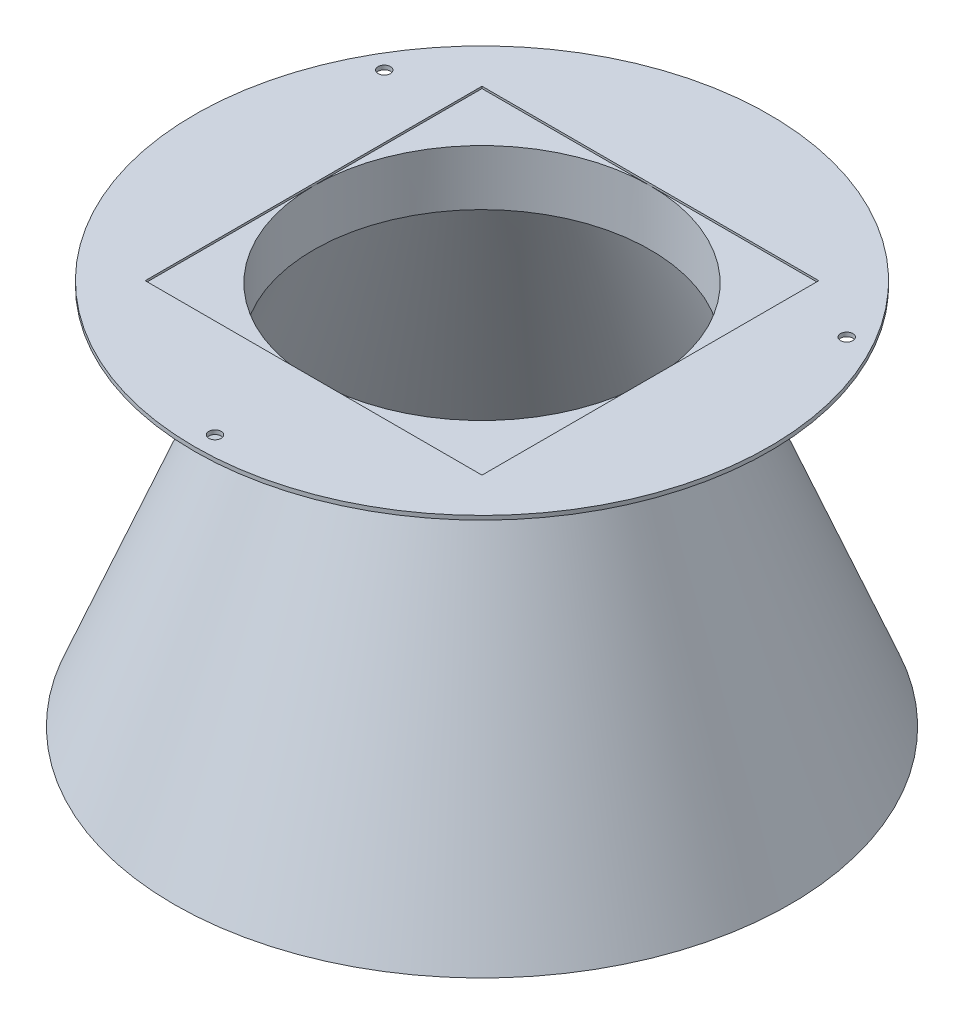
SolidWorks part; units mm, degrees
ref_plane "Alzado" through (0, 0, 0) normal (0, 0, 1) x (1, 0, 0)
ref_plane "Planta" through (0, 0, 0) normal (0, 1, 0) x (1, 0, 0)
ref_plane "Vista lateral" through (0, 0, 0) normal (1, 0, 0) x (0, 0, -1)
sketch "Croquis1" plane through (0, 0, 0) normal (0, 0, 1) x (1, 0, 0)
  line L0 (-67.9016, 46.9761) -> (-67.9016, 60.9761)
  line L1 (-69.9016, 46.9761) -> (-69.9016, -33.0239) construction
  line L2 (-67.9016, 46.9761) -> (14.0984, 46.9761) construction
  line L3 (-26.9016, 46.9761) -> (-26.9016, -33.0239) construction
  line L4 (-26.9016, -33.0239) -> (-101.9016, -33.0239) construction
  line L5 (-69.9016, 46.9761) -> (-101.9016, -33.0239)
  line L6 (-101.9016, -33.0239) -> (-99.9016, -33.0239)
  line L7 (-99.9016, -33.0239) -> (-67.9016, 46.9761)
  line L8 (-26.9016, 46.9761) -> (-26.9016, 61.9761) construction
  line L9 (-26.9016, 61.9761) -> (-86.9016, 61.9761) construction
  line L10 (-96.9016, 60.9761) -> (-67.9016, 60.9761)
  line L12 (-96.9016, 59.9761) -> (-86.9016, 59.9761)
  line L13 (-96.9016, 60.9761) -> (-96.9016, 59.9761)
  line L14 (-86.9016, 59.9761) -> (-69.9016, 46.9761)
revolve "Revolución1" add sketch "Croquis1" angle 360 about L3
sketch "Croquis6" plane through (0, 59.9761, 0) normal (0, -1, 0) x (1, 0, 0)
  circle A0 centre (-26.9016, 65) radius 1.5
  circle A1 centre (29.39, -32.5) radius 1.5
  circle A2 centre (-83.1933, -32.5) radius 1.5
extrude "Cortar-Extruir9" cut sketch "Croquis6" against normal blind 10
sketch "Croquis2" plane through (0, 71.9761, 0) normal (0, 1, 0) x (1, 0, 0)
  line L1 (14.0984, -41) -> (-67.9016, -41)
  line L2 (14.0984, -41) -> (14.0984, 41)
  line L3 (14.0984, 41) -> (-67.9016, 41)
  line L4 (-67.9016, -41) -> (-67.9016, 41)
  line L5 (14.0984, -41) -> (-67.9016, 41) construction
  line L6 (14.0984, 41) -> (-67.9016, -41) construction
  point P0 (-26.9016, 0)
  dimension "D1" = 82
  dimension "D2" = 82
extrude "Cortar-Extruir1" cut sketch "Croquis2" against normal blind 11.5
sketch "Croquis3" plane through (0, 71.9761, 0) normal (0, 1, 0) x (1, 0, 0)
  line L0 (14.0984, -41) -> (14.0984, 41) construction
  line L3 (32.4195, 9) -> (25.0984, 9)
  line L4 (25.0984, 9) -> (25.0984, -9)
  line L5 (25.0984, -9) -> (32.4195, -9)
  arc A2 (32.4195, 9) -> (32.4195, -9) centre (-26.9016, 0) cw
sketch "Croquis4" plane through (25.0984, 0, 0) normal (-1, 0, 0) x (0, 0, 1)
  line L0 (-9, 71.9761) -> (9, 82.4761) construction
  line L1 (9, 82.4761) -> (9, 71.9761) construction
  line L2 (9, 71.9761) -> (-9, 82.4761) construction
  line L4 (-7, 81.4761) -> (7, 81.4761)
  line L5 (-7, 81.4761) -> (-7, 72.9761)
  line L6 (-7, 72.9761) -> (7, 72.9761)
  line L7 (7, 81.4761) -> (7, 72.9761)
  line L8 (-7, 81.4761) -> (7, 72.9761) construction
  line L9 (-7, 72.9761) -> (7, 81.4761) construction
  point P6 (0, 77.2261)
  dimension "D1" = 14
  dimension "D2" = 8.5
extrude "Cortar-Extruir2" cut sketch "Croquis4" against normal blind 10.5
